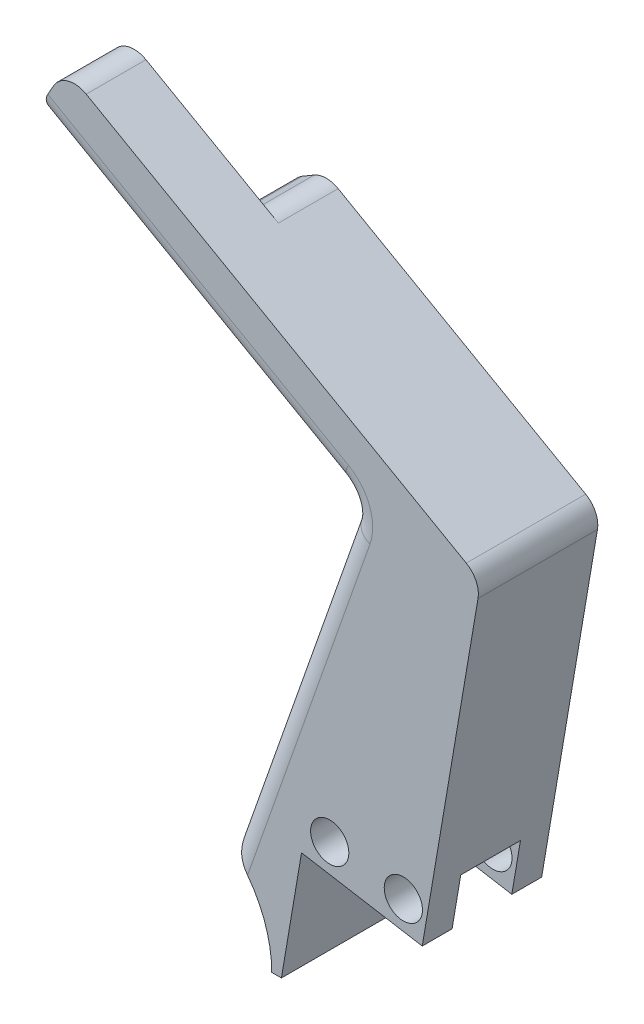
SolidWorks part; units mm, degrees
ref_plane "Front Plane" through (0, 0, 0) normal (0, 0, 1) x (1, 0, 0)
ref_plane "Top Plane" through (0, 0, 0) normal (0, 1, 0) x (1, 0, 0)
ref_plane "Right Plane" through (0, 0, 0) normal (1, 0, 0) x (0, 0, -1)
sketch "Sketch3" plane through (0, 0, 0) normal (0, 0, 1) x (1, 0, 0)
  line L0 (-58.011, 64.7137) -> (-70.8453, 66.8904)
  line L1 (-71.5428, 47.0107) -> (-86.7102, 40.4535)
  line L2 (-70.8453, 66.8904) -> (-64.6168, 103.614) construction
  line L3 (-86.7102, 40.4535) -> (-101.8777, 47.0107)
  line L4 (-64.6168, 103.614) -> (-51.7826, 101.4373) construction
  line L5 (-51.7826, 101.4373) -> (-58.011, 64.7137)
  line L6 (-74.0102, 54.2895) -> (-72.9824, 54.2895)
  line L7 (-78.5468, 64.0182) -> (-86.7102, 54.2895) construction
  line L8 (-74.0102, 54.2895) -> (-99.4102, 54.2895) construction
  line L9 (-64.6168, 103.614) -> (-78.5468, 64.0182)
  line L16 (-71.2908, 46.4278) -> (-85.8329, 40.141)
  line L17 (-74.2958, 31.7751) -> (-66.6826, 34.2679)
  line L18 (-106.7378, 34.2679) -> (-99.1247, 31.7751)
  line L19 (-87.5876, 40.141) -> (-102.1296, 46.4278)
  line L20 (-87.5876, 40.141) -> (-85.8329, 40.141)
  line L21 (-51.7826, 101.4373) -> (-95.9416, 126.5496)
  line L22 (-69.9259, 72.311) -> (-64.9545, 101.6229)
  line L23 (-64.9545, 101.6229) -> (-99.0806, 121.0297)
  line L24 (-95.9416, 126.5496) -> (-99.0806, 121.0297)
  line L25 (-98.2954, 41.5418) -> (-103.4983, 72.2187)
  line L26 (-103.4983, 72.2187) -> (-116.3325, 70.042)
  line L27 (-116.3325, 70.042) -> (-111.1296, 39.3651)
  line L31 (-57.0917, 70.1343) -> (-69.9259, 72.311)
  line L32 (-69.9259, 72.311) -> (-75.1288, 41.6341)
  line L33 (-62.2946, 39.4574) -> (-57.0917, 70.1343)
  circle A0 centre (-86.7102, 54.2895) radius 12.7
  arc A1 (-86.7102, 66.9895) -> (-74.2349, 56.6676) centre (-86.7102, 54.2895) cw
  arc A2 (-86.7102, 66.9895) -> (-74.2234, 56.6065) centre (-86.7102, 54.2895) ccw
  arc A3 (-86.7102, 66.9895) -> (-74.2492, 56.7414) centre (-86.7102, 54.2895) cw
  arc A6 (-66.6826, 34.2679) -> (-71.2908, 46.4278) centre (-68.708, 40.4535) ccw
  arc A7 (-102.1296, 46.4278) -> (-106.7378, 34.2679) centre (-104.7125, 40.4535) ccw
  arc A8 (-78.5468, 64.0182) -> (-74.0102, 54.2895) centre (-86.7102, 54.2895) cw
  arc A10 (-111.1296, 39.3651) -> (-98.2954, 41.5418) centre (-104.7125, 40.4535) ccw
  circle A11 centre (-107.8979, 59.2352) radius 3.5306
  circle A13 centre (-113.4035, 67.9625) radius 2.032
  circle A15 centre (-105.5778, 69.2898) radius 2.032
  circle A16 centre (-68.708, 40.4535) radius 2.5845
  circle A17 centre (-104.7162, 40.5458) radius 2.5845
  arc A27 (-75.1288, 41.6341) -> (-62.2946, 39.4574) centre (-68.7117, 40.5458) ccw
  circle A30 centre (-60.0206, 68.0548) radius 2.032
  circle A31 centre (-67.8464, 69.3821) radius 2.032
  circle A32 centre (-65.5225, 59.2352) radius 3.5306
  spline S2 degree 3 poles (-85.8329, 40.141) (-85.5852, 39.9689) (-85.3576, 39.774) (-84.9098, 39.3759) (-84.6911, 39.171) (-84.0382, 38.5527) (-83.6074, 38.1355) (-82.2996, 36.9011) (-81.4086, 36.0998) (-80.0016, 34.9777) (-79.5208, 34.6166) (-78.5406, 33.9331) (-78.0401, 33.6097) (-76.5028, 32.7035) (-75.4305, 32.1837) (-74.2958, 31.7751) knots 0 0 0 0 0.0625 0.0625 0.125 0.125 0.25 0.25 0.5 0.5 0.625 0.625 0.75 0.75 1 1 1 1
  spline S3 degree 3 poles (-99.1247, 31.7751) (-97.9892, 32.1839) (-96.9172, 32.7038) (-94.869, 33.9111) (-93.8919, 34.6007) (-92.0143, 36.0977) (-91.1227, 36.8994) (-89.8143, 38.1344) (-89.3832, 38.5518) (-88.73, 39.1704) (-88.5112, 39.3754) (-88.0632, 39.7737) (-87.8355, 39.9687) (-87.5876, 40.141) knots 0 0 0 0 0.25 0.25 0.5 0.5 0.75 0.75 0.875 0.875 0.9375 0.9375 1 1 1 1
  point P45 (-87.5876, 99.2837)
  point P52 (-78.5468, 64.0182)
  dimension "D1" = 25.4
  dimension "D2" = 31.75
  dimension "D3" = 13.0175
  dimension "D4" = 5.498
  dimension "D5" = 50
  dimension "D6" = 250
  dimension "D7" = 6.35
  dimension "D8" = 50.8
extrude "Boss-Extrude1" add sketch "Sketch3" along normal blind 12.7 contours L31 L5 L4 L2 | A0 L6 L32 L2 L9 A1 | L5 L31 L2 L0 A31 A30
sketch "Sketch4" plane through (-67.0578, 11.3732, 0) normal (0.9859, -0.1672, 0) x (0, 0, -1)
  line L1 (0, 91.3502) -> (0, 54.1022) construction
  line L2 (-12.7, 54.1022) -> (0, 54.1022) construction
  line L3 (-12.7, 91.3502) -> (-12.7, 54.1022) construction
  line L4 (-12.7, 91.3502) -> (0, 91.3502)
  line L5 (0, 91.3502) -> (0, 54.1022)
  line L6 (-12.7, 54.1022) -> (0, 54.1022)
  line L7 (-12.7, 91.3502) -> (-12.7, 54.1022)
  line L8 (-12.7, 59.6002) -> (0, 59.6002)
  line L9 (-9.525, 59.6002) -> (-9.525, 54.1022)
  line L10 (-3.175, 59.6002) -> (-3.175, 54.1022)
  point P10 (-9.525, 56.8512)
  dimension "D1" = 31.75
  dimension "D2" = 3.175
  dimension "D3" = 3.175
extrude "Cut-Extrude1" cut sketch "Sketch4" against normal up to surface (13.0175 mm away) contours L10 L8 L9 L6 up to face at (-71.9138, 60.59, 6.35)
sketch "Sketch5" plane through (0, 0, 0) normal (0, 0, -1) x (-1, 0, 0)
  line L0 (99.0806, 121.0297) -> (95.9416, 126.5496)
  line L2 (51.7826, 101.4373) -> (95.9416, 126.5496) construction
  line L4 (65.2568, 101.7948) -> (99.0806, 121.0297) construction
  line L6 (87.2534, 114.3038) -> (80.9275, 118.0114)
  line L7 (80.9275, 118.0114) -> (95.9416, 126.5496)
  line L8 (87.2534, 114.3038) -> (99.0806, 121.0297)
  dimension "D1" = 120
  dimension "D2" = 17.272
extrude "Cut-Extrude2" cut sketch "Sketch5" against normal blind 6.35
fillet "Fillet1" radius 2.54 11 edges at (-87.2534, 114.3038, 3.175) (-82.1687, 111.4122, 12.7) (-76.2551, 108.0493, 0) (-65.2568, 101.7948, 6.35) (-71.9018, 82.9065, 0) (-71.9018, 82.9065, 12.7) (-78.5468, 64.0182, 6.35) (-51.7826, 101.4373, 6.35) (-80.9275, 118.0114, 3.175) (-95.9416, 126.5496, 9.525) (-99.0806, 121.0297, 9.525)
